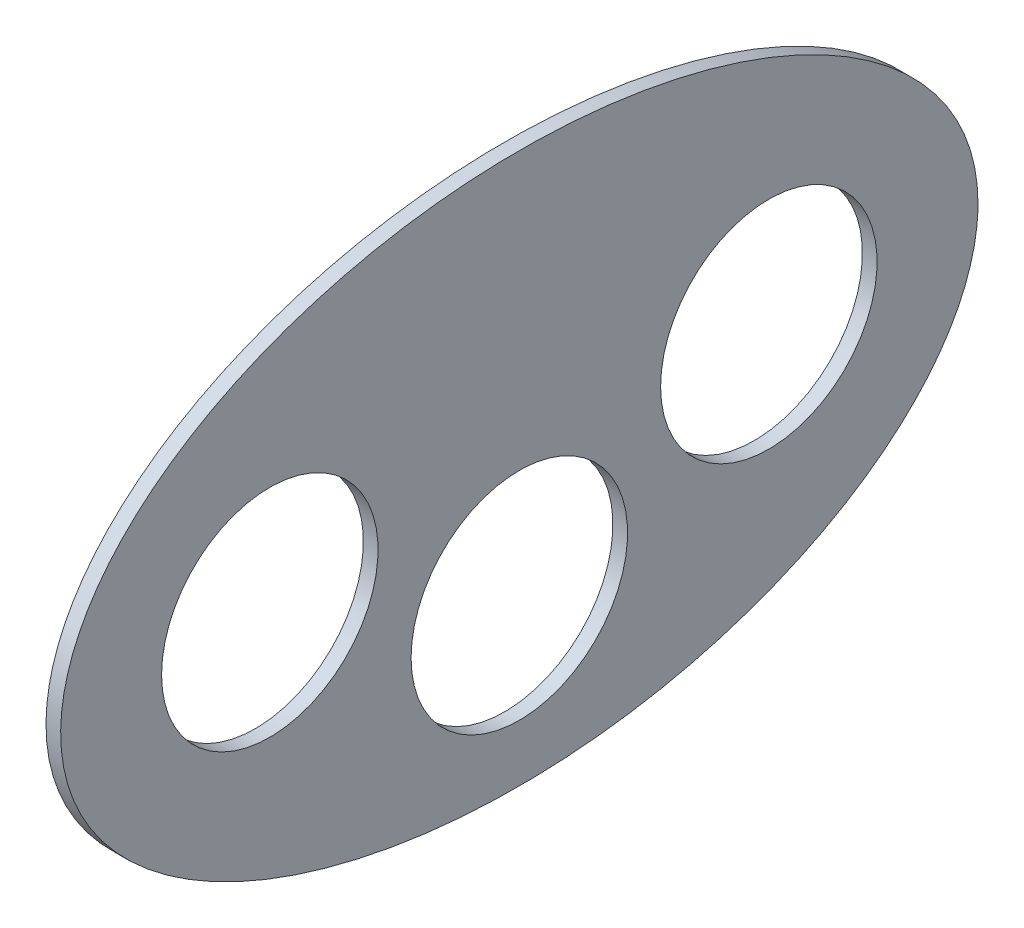
SolidWorks part; units mm, degrees
ref_plane "Front Plane" through (0, 0, 0) normal (0, 0, 1) x (1, 0, 0)
ref_plane "Top Plane" through (0, 0, 0) normal (0, 1, 0) x (1, 0, 0)
ref_plane "Right Plane" through (0, 0, 0) normal (1, 0, 0) x (0, 0, -1)
sketch "Sketch1" plane through (0, 0, 0) normal (1, 0, 0) x (0, 0, -1)
  ellipse E0 centre (0, 0) end of major axis (125, 0) minor radius 75
  dimension "D1" = 250
  dimension "D2" = 150
extrude "Boss-Extrude1" add sketch "Sketch1" along normal blind 4
sketch "Sketch2" plane through (0, 0, 0) normal (-1, 0, 0) x (0, 0, 1)
  circle A0 centre (68, 0) radius 29.5
  circle A1 centre (-68, 0) radius 29.5
  circle A2 centre (0, -30) radius 29.5
  dimension "D1" = 59
  dimension "D2" = 68
  dimension "D3" = 68
  dimension "D4" = 30
extrude "Cut-Extrude1" cut sketch "Sketch2" against normal through all
